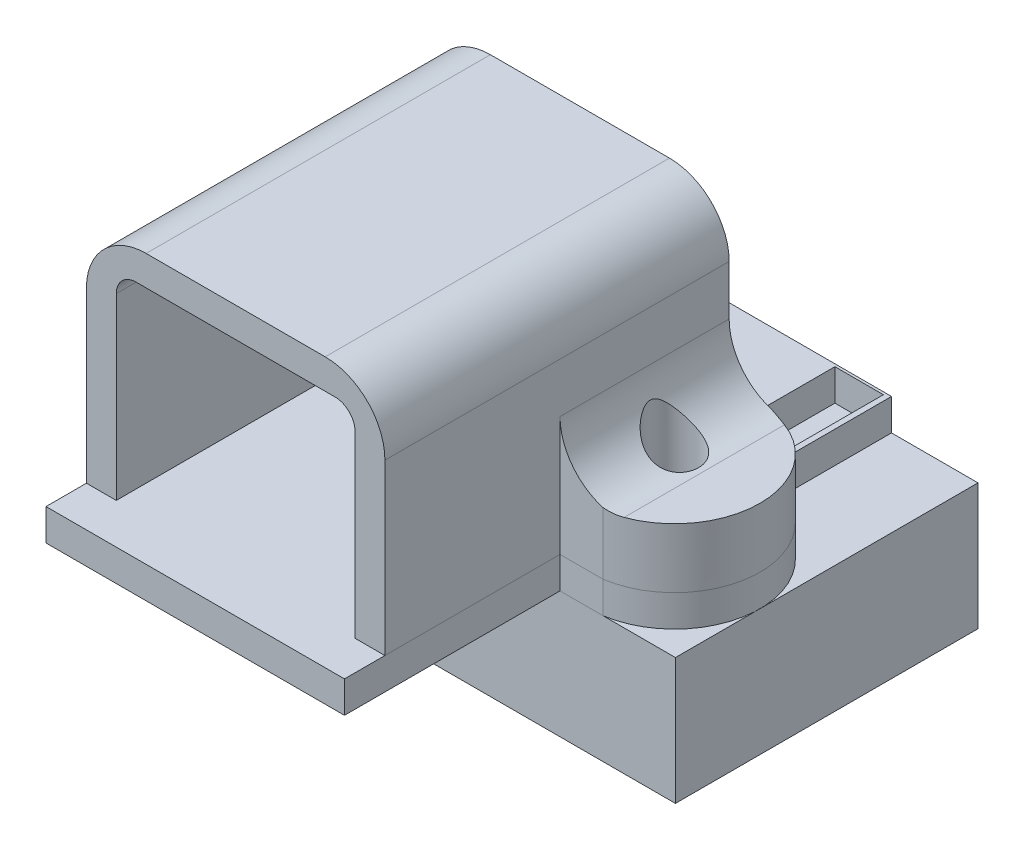
SolidWorks part; units mm, degrees
material "ABS"
ref_plane "Front Plane" through (0, 0, 0) normal (0, 0, 1) x (1, 0, 0)
ref_plane "Top Plane" through (0, 0, 0) normal (0, 1, 0) x (1, 0, 0)
ref_plane "Right Plane" through (0, 0, 0) normal (1, 0, 0) x (0, 0, -1)
sketch "Sketch1" plane through (0, 0, 0) normal (0, 0, 1) x (1, 0, 0)
  line L0 (-13.3, 0) -> (-6, 0)
  line L1 (-13.3, 0) -> (-13.3, 3)
  line L2 (-13.3, 3) -> (-10.5, 3)
  line L3 (-7.5, 6) -> (-7.5, 8.5)
  line L4 (-4.5, 11.5) -> (4.5, 11.5)
  line L5 (0, 11.5) -> (0, 0) construction
  line L6 (7.5, 6) -> (7.5, 8.5)
  line L7 (13.3, 3) -> (10.5, 3)
  line L8 (13.3, 0) -> (13.3, 3)
  line L9 (-6, 0) -> (-6, 9)
  line L10 (-5, 10) -> (5, 10)
  line L11 (6, 0) -> (6, 9)
  line L12 (6, 0) -> (13.3, 0)
  arc A0 (7.5, 8.5) -> (4.5, 11.5) centre (4.5, 8.5) ccw
  arc A1 (-7.5, 8.5) -> (-4.5, 11.5) centre (-4.5, 8.5) cw
  arc A2 (-10.5, 3) -> (-7.5, 6) centre (-10.5, 6) ccw
  arc A3 (7.5, 6) -> (10.5, 3) centre (10.5, 6) ccw
  arc A4 (-6, 9) -> (-5, 10) centre (-5, 9) cw
  arc A5 (6, 9) -> (5, 10) centre (5, 9) ccw
  point P13 (7.5, 11.5)
  point P16 (-7.5, 11.5)
  point P19 (-7.5, 3)
  point P22 (7.5, 3)
  point P31 (0, 10)
  dimension "D5" = 3
  dimension "D8" = 1
  dimension "D1" = 26.6
  dimension "D2" = 15
  dimension "D3" = 11.5
  dimension "D4" = 3
  dimension "D6" = 12
  dimension "D7" = 1.5
extrude "Extrude1" add sketch "Sketch1" along normal blind 17.3
sketch "Sketch2" plane through (0, 0, 17.3) normal (0, 0, 1) x (1, 0, 0)
  line L1 (-13.3, 0) -> (-6, 0) construction
  line L2 (-13.3, 0) -> (-7.5, 0)
  line L3 (-13.3, 0) -> (-13.3, 8.5)
  line L4 (-13.3, 8.5) -> (-7.5, 8.5)
  line L6 (-7.5, 0) -> (-7.5, 8.5)
  line L7 (-13.3, 3) -> (-13.3, 0) construction
  line L9 (13.3, 0) -> (7.5, 0)
  line L10 (13.3, 0) -> (13.3, 8.5)
  line L11 (13.3, 8.5) -> (7.5, 8.5)
  line L12 (7.5, 0) -> (7.5, 8.5)
extrude "Extrude2" cut sketch "Sketch2" against normal blind 8.8
sketch "Sketch3" plane through (0, 0, 0) normal (0, -1, 0) x (1, 0, 0)
  line L2 (7.5, 8.5) -> (13.3, 8.5) construction
  line L3 (6, 0) -> (13.3, 0) construction
  line L4 (13.3, 8.5) -> (13.3, 0) construction
  line L5 (9.6538, 8.5) -> (9.6538, 9.263)
  line L6 (9.6538, 9.263) -> (15.0793, 9.263)
  line L7 (15.0793, 9.263) -> (15.0793, -0.4862)
  line L8 (15.0793, -0.4862) -> (9.6538, -0.4862)
  line L9 (9.6538, -0.4862) -> (9.6538, 0)
  line L10 (0, 17.3) -> (0, 0) construction
  line L11 (-5, 17.3) -> (5, 17.3) construction
  line L12 (-9.6538, -0.4862) -> (-9.6538, 0)
  line L13 (-15.0793, -0.4862) -> (-9.6538, -0.4862)
  line L14 (-15.0793, 9.263) -> (-15.0793, -0.4862)
  line L15 (-9.6538, 9.263) -> (-15.0793, 9.263)
  line L16 (-9.6538, 8.5) -> (-9.6538, 9.263)
  arc A0 (9.6538, 8.5) -> (9.6538, 0) centre (9, 4.25) cw
  arc A1 (-9.6538, 8.5) -> (-9.6538, 0) centre (-9, 4.25) ccw
  circle A2 centre (-9, 4.25) radius 1
  circle A3 centre (9, 4.25) radius 1
  dimension "D1" = 2
  dimension "D2" = 18
extrude "Extrude3" cut sketch "Sketch3" against normal blind 5
hole_wizard "#2 Clearance Hole1" positions "3DSketch1" profile "Sketch4" hole size "#2" standard "Ansi Inch" end condition up to next
sketch3d "3DSketch1"
  line L0 (-9, 3.5214, 4.25) -> (-9, 0, 4.25) construction
  line L1 (9, 3.5201, 4.25) -> (9, 0, 4.25) construction
  point P0 (-9, 0, 4.25)
  point P2 (9, 0, 4.25)
sketch "Sketch4" plane through (-9, 0, 4.25) normal (1, 0, 0) x (0, 0, -1)
  line L0 (0, 0) -> (0, 11.5)
  line L1 (0, 11.5) -> (1.2192, 11.5)
  line L2 (1.2192, 11.5) -> (1.2192, 0)
  line L5 (1.2192, 0) -> (0, 0)
  line L11 (0, -6.35) -> (0, 107.95) construction
  dimension "Thru Hole Dia." = 2.4384
  dimension "Thru Hole Depth" = 11.5
sketch "Sketch5" plane through (0, 0, 0) normal (0, -1, 0) x (1, 0, 0)
  line L0 (-8.9535, -6.7056) -> (-8.9535, 0)
  line L1 (-8.9535, -6.7056) -> (8.9535, -6.7056)
  line L2 (-9.6538, 0) -> (-6, 0) construction
  line L3 (-5, 0) -> (5, 0) construction
  line L4 (0, 17.3) -> (0, -6.7056) construction
  line L5 (-8.6741, -1.4986) -> (-6.2357, -1.4986)
  line L6 (-8.6741, -1.4986) -> (-8.6741, -6.5786)
  line L7 (-8.6741, -6.5786) -> (-6.2357, -6.5786)
  line L8 (-6.2357, -1.4986) -> (-6.2357, -6.5786)
  line L9 (6.2357, -1.4986) -> (8.6741, -1.4986)
  line L10 (6, 0) -> (9.6538, 0)
  line L11 (9.6538, 8.5) -> (7.5, 8.5)
  line L12 (7.5, 8.5) -> (7.5, 17.3)
  line L13 (7.5, 17.3) -> (6, 17.3)
  line L14 (6, 17.3) -> (6, 0)
  line L15 (8.9535, 0) -> (9.6538, 0)
  line L16 (9.6538, 8.5) -> (7.5, 8.5)
  line L17 (7.5, 8.5) -> (7.5, 19.332)
  line L18 (-7.5, 19.332) -> (7.5, 19.332)
  line L19 (6.2357, -1.4986) -> (6.2357, -6.5786)
  line L20 (6.2357, -6.5786) -> (8.6741, -6.5786)
  line L21 (8.6741, -1.4986) -> (8.6741, -6.5786)
  line L22 (-6.2357, -4.0386) -> (6.2357, -4.0386) construction
  line L23 (-5, 17.3) -> (5, 17.3) construction
  line L24 (8.9535, -6.7056) -> (8.9535, 0)
  line L25 (-7.5, 8.5) -> (-9.6538, 8.5)
  line L26 (-9.6538, 0) -> (-6, 0)
  line L27 (-6, 0) -> (-6, 17.3)
  line L28 (-6, 17.3) -> (-7.5, 17.3)
  line L29 (-7.5, 17.3) -> (-7.5, 8.5)
  line L30 (-7.5, 8.5) -> (-9.6538, 8.5)
  line L31 (-9.6538, 0) -> (-8.9535, 0)
  line L32 (-7.4549, -1.4986) -> (-7.4549, -6.5786) construction
  line L34 (-7.5, 19.332) -> (-7.5, 8.5)
  line L35 (7.4549, -6.5786) -> (7.4549, -1.4986) construction
  arc A2 (9.6538, 0) -> (9.6538, 8.5) centre (9, 4.25) ccw
  arc A3 (9.6538, 0) -> (9.6538, 8.5) centre (9, 4.25) ccw
  arc A5 (-9.6538, 8.5) -> (-9.6538, 0) centre (-9, 4.25) ccw
  arc A6 (-9.6538, 8.5) -> (-9.6538, 0) centre (-9, 4.25) ccw
  circle A8 centre (9, 4.25) radius 1.2192
  circle A9 centre (9, 4.25) radius 1.2192
  circle A11 centre (-9, 4.25) radius 1.2192
  circle A12 centre (-9, 4.25) radius 1.2192
  point P40 (0, -4.0386)
  dimension "D5" = 6.7056
  dimension "D6" = 5.08
  dimension "D7" = 2.4384
  dimension "D8" = 17.907
  dimension "D9" = 2.032
  dimension "D10" = 14.9098
  dimension "D11" = 2.667
  dimension "D1" = 0
  dimension "D2" = 0
  dimension "D3" = 0
  dimension "D4" = 0
extrude "Extrude4" add sketch "Sketch5" along normal blind 1.5875 separate body
sketch "Sketch6" plane through (0, -1.5875, 0) normal (0, -1, 0) x (1, 0, 0)
  line L1 (8.6741, -6.5786) -> (6.2357, -6.5786)
  line L2 (8.6741, -6.5786) -> (8.6741, -1.4986)
  line L3 (8.6741, -1.4986) -> (6.2357, -1.4986)
  line L4 (6.2357, -6.5786) -> (6.2357, -1.4986)
  line L5 (-6.2357, -6.5786) -> (-8.6741, -6.5786)
  line L6 (-6.2357, -6.5786) -> (-6.2357, -1.4986)
  line L7 (-6.2357, -1.4986) -> (-8.6741, -1.4986)
  line L8 (-8.6741, -6.5786) -> (-8.6741, -1.4986)
extrude "Extrude5" add sketch "Sketch6" along normal blind 1.27 separate body
sketch "Sketch7" plane through (0, -2.8575, 0) normal (0, -1, 0) x (1, 0, 0)
  line L0 (0, -6.7056) -> (0, 0) construction
  line L1 (-8.9535, -6.7056) -> (8.9535, -6.7056) construction
  line L2 (-7.4549, -1.4986) -> (-7.4549, -6.5786) construction
  line L3 (-6.2357, -1.4986) -> (-8.6741, -1.4986) construction
  line L4 (-8.6741, -6.5786) -> (-6.2357, -6.5786) construction
  circle A0 centre (-7.4549, -2.4254) radius 0.381
  circle A1 centre (-7.4549, -5.7337) radius 0.381
  circle A2 centre (7.4549, -5.7337) radius 0.381
  circle A3 centre (7.4549, -2.4254) radius 0.381
  dimension "D1" = 0.762
extrude "Extrude6" add sketch "Sketch7" along normal blind 8.128 separate body
sketch "Sketch8" plane through (0, -1.5875, 0) normal (0, -1, 0) x (1, 0, 0)
  line L0 (-8.9535, -6.7056) -> (8.9535, -6.7056) construction
  line L1 (-13.3, 8.5) -> (13.3, 8.5)
  line L2 (-13.3, 8.5) -> (-13.3, -6.7056)
  line L3 (-13.3, -6.7056) -> (-8.8088, -6.7056)
  line L4 (13.3, 8.5) -> (13.3, -6.7056)
  line L7 (-7.5, 8.5) -> (-9.6538, 8.5) construction
  line L8 (0, 0) -> (0, -6.7056) construction
  line L9 (-8.8088, -1.3082) -> (-6.0803, -1.3082)
  line L10 (-8.8088, -1.3082) -> (-8.8088, -6.7056)
  line L11 (8.8088, -6.7056) -> (13.3, -6.7056)
  line L12 (-6.0803, -1.3082) -> (-6.0803, -6.7056)
  line L13 (6.0803, -1.3082) -> (6.0803, -6.7056)
  line L15 (8.8088, -1.3082) -> (8.8088, -6.7056)
  line L16 (8.8088, -1.3082) -> (6.0803, -1.3082)
  line L17 (-6.0803, -6.7056) -> (6.0803, -6.7056)
  arc A0 (-9.6538, 8.5) -> (-9.6538, 0) centre (-9, 4.25) ccw construction
  circle A1 centre (-9, 4.25) radius 1.2192
  circle A2 centre (9, 4.25) radius 1.2192
  point P6 (0, 8.5)
extrude "Extrude7" add sketch "Sketch8" along normal blind 6.35 separate body
